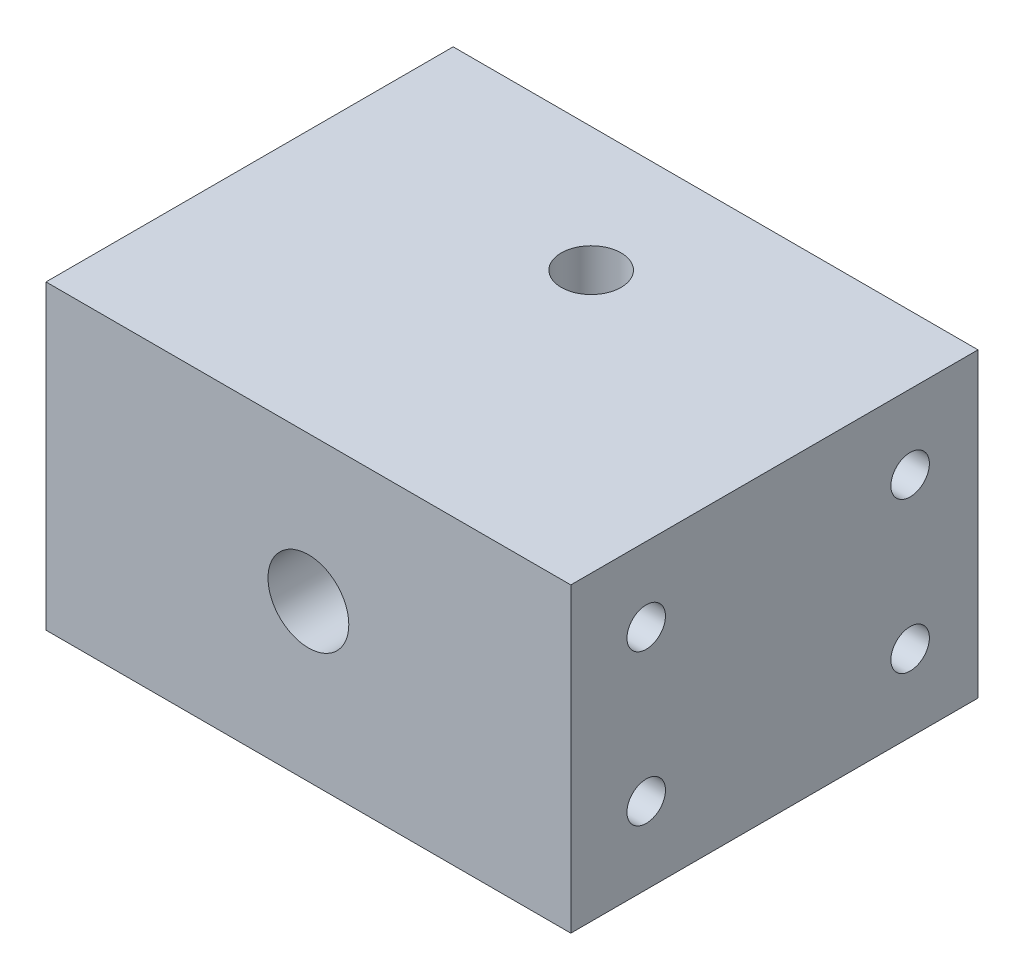
SolidWorks part; units mm, degrees
material "6061 Alloy"
ref_plane "Front Plane" through (0, 0, 0) normal (0, 0, 1) x (1, 0, 0)
ref_plane "Top Plane" through (0, 0, 0) normal (0, 1, 0) x (1, 0, 0)
ref_plane "Right Plane" through (0, 0, 0) normal (1, 0, 0) x (0, 0, -1)
sketch "Sketch1" plane through (0, 0, 0) normal (0, 1, 0) x (1, 0, 0)
  line L0 (-34.8, -37.5) -> (34.8, 37.5) construction
  line L1 (-34.8, 37.5) -> (34.8, 37.5)
  line L2 (-34.8, 37.5) -> (-34.8, -37.5)
  line L3 (-34.8, -37.5) -> (34.8, -37.5)
  line L4 (34.8, 37.5) -> (34.8, -37.5)
  dimension "D1" = 75
  dimension "D2" = 69.6
extrude "Boss-Extrude1" add sketch "Sketch1" along normal blind 40
sketch "Sketch3" plane through (0, 0, 0) normal (0, 1, 0) x (1, 0, 0)
  line L1 (54.2912, 16.5) -> (54.2912, 59.1473)
  line L2 (54.2912, 59.1473) -> (-72.7007, 59.1473)
  line L3 (-72.7007, 59.1473) -> (-72.7007, 16.5)
  line L4 (-72.7007, 16.5) -> (54.2912, 16.5)
  line L5 (-34.8, -37.5) -> (34.8, -37.5) construction
  dimension "D1" = 54
extrude "Cut-Extrude2" cut sketch "Sketch3" along normal through all
hole_wizard "3/8-16 Tapped Hole1" positions "Sketch7" profile "Sketch8" tap size "3/8-16" standard "ANSI Inch"
sketch "Sketch7" plane through (0, 40, 0) normal (0, 1, 0) x (1, 0, 0)
  point P0 (0, 0)
sketch "Sketch8" plane through (0, 40, 0) normal (1, 0, 0) x (0, 0, 1)
  line L0 (0, 0) -> (0, 18.2597)
  line L1 (0, 18.2597) -> (3.9687, 15.875)
  line L2 (3.9687, 15.875) -> (3.9687, 0)
  line L5 (3.9687, 0) -> (0, 0)
  line L10 (0, 18.2597) -> (-3.9688, 15.875) construction
  line L11 (0, -6.35) -> (0, 107.95) construction
  dimension "Tap Drill Dia." = 7.9375
  dimension "Tap Drill Depth" = 15.875
  dimension "Drill Angle" = 118
hole_wizard "1/4-20 Tapped Hole1" positions "Sketch9" profile "Sketch10" tap size "1/4-20" standard "ANSI Inch"
sketch "Sketch9" plane through (34.8, 0, 0) normal (1, 0, 0) x (0, 0, -1)
  line L1 (7.5, 30.16) -> (-27.5, 30.16) construction
  line L2 (-27.5, 30.16) -> (-27.5, 10.16) construction
  line L3 (-27.5, 10.16) -> (7.5, 10.16) construction
  line L4 (7.5, 10.16) -> (7.5, 30.5312) construction
  line L7 (-37.5, 0) -> (16.5, 0) construction
  line L8 (-37.5, 40) -> (-37.5, 0) construction
  point P0 (7.5, 30.16)
  point P2 (7.5, 10.16)
  point P4 (-27.5, 10.16)
  point P6 (-27.5, 30.16)
  dimension "D1" = 20
  dimension "D2" = 35
  dimension "D3" = 10
  dimension "D4" = 10.16
sketch "Sketch10" plane through (34.8, 30.16, -7.5) normal (0, 1, 0) x (0, 0, -1)
  line L0 (0, 0) -> (0, 14.5338)
  line L1 (0, 14.5338) -> (2.5527, 13)
  line L2 (2.5527, 13) -> (2.5527, 0)
  line L5 (2.5527, 0) -> (0, 0)
  line L10 (0, 14.5338) -> (-2.5527, 13) construction
  line L11 (0, -6.35) -> (0, 107.95) construction
  dimension "Tap Drill Dia." = 5.1054
  dimension "Tap Drill Depth" = 13
  dimension "Drill Angle" = 118
mirror "Mirror1" about plane through (0, 0, 0) normal (1, 0, 0) of "1/4-20 Tapped Hole1"
sketch "Sketch11" plane through (0, 0, 0) normal (1, 0, 0) x (0, 0, -1)
  line L0 (20.1127, 20.9966) -> (-33.5, -4.0034)
  line L1 (-33.5, -4.0034) -> (20.1127, -4.0034)
  line L2 (20.1127, -4.0034) -> (20.1127, 20.9966)
  line L3 (16.5, 40) -> (16.5, 0) construction
  dimension "D1" = 50
  dimension "D2" = 25
  dimension "D3" = 25
extrude "Cut-Extrude3" cut sketch "Sketch11" against normal mid plane 40
hole_wizard "1/2-13 Tapped Hole1" positions "Sketch12" profile "Sketch13" tap size "1/2-13" standard "ANSI Inch"
sketch "Sketch12" plane through (0, 0, 37.5) normal (0, 0, 1) x (1, 0, 0)
  line L0 (0, 1.4377) -> (0, 40)
  line L1 (-34.8, 40) -> (34.8, 40) construction
  point P0 (0, 20.7189)
  point P8 (0, 20.7189)
sketch "Sketch13" plane through (0, 20.7189, 37.5) normal (1, 0, 0) x (0, -1, 0)
  line L0 (0, 0) -> (0, 28.2195)
  line L1 (0, 28.2195) -> (5.3581, 25)
  line L2 (5.3581, 25) -> (5.3581, 0)
  line L5 (5.3581, 0) -> (0, 0)
  line L10 (0, 28.2195) -> (-5.3581, 25) construction
  line L11 (0, -6.35) -> (0, 107.95) construction
  dimension "Tap Drill Dia." = 10.7163
  dimension "Tap Drill Depth" = 25
  dimension "Drill Angle" = 118
fillet "Fillet1" radius 2 2 edges at (-20, 9.656, 4.2074) (20, 9.656, 4.2074)
